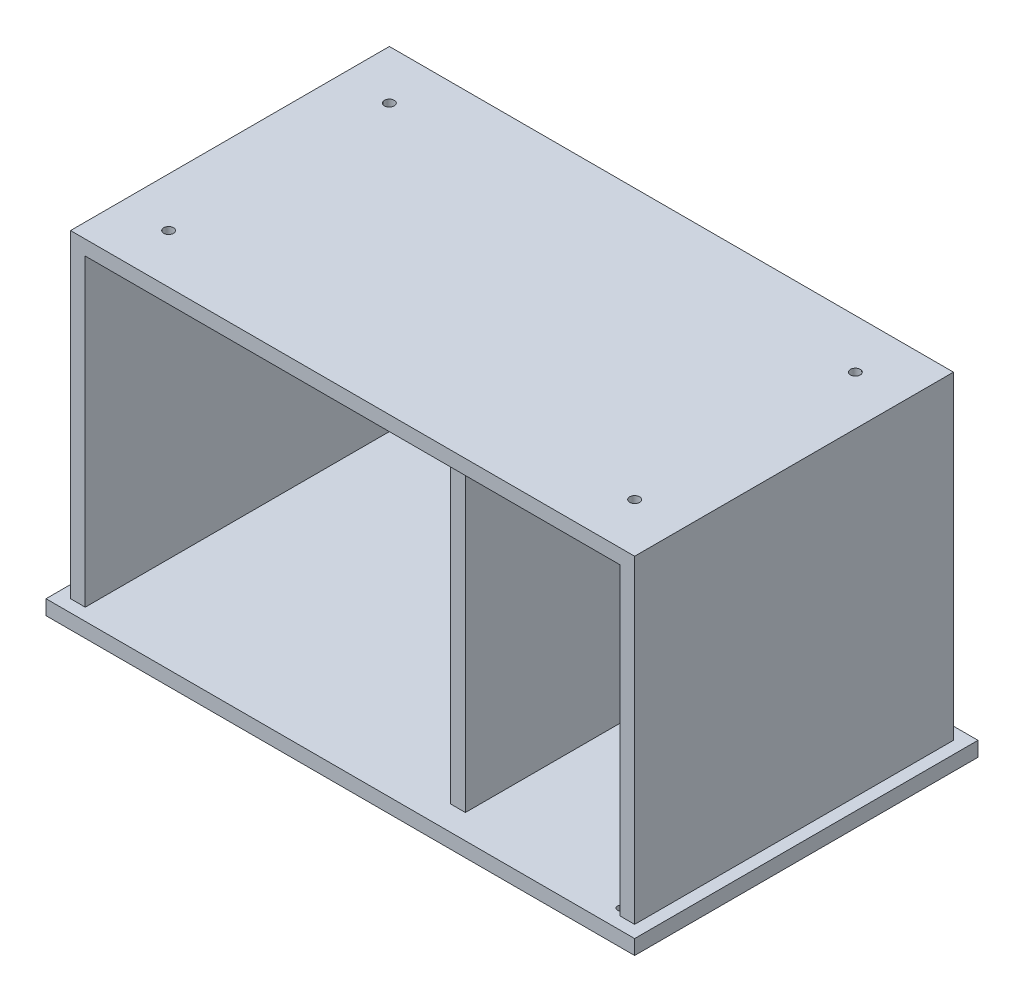
SolidWorks part; units mm, degrees
material "Oak"
ref_plane "Front Plane" through (0, 0, 0) normal (0, 0, 1) x (1, 0, 0)
ref_plane "Top Plane" through (0, 0, 0) normal (0, 1, 0) x (1, 0, 0)
ref_plane "Right Plane" through (0, 0, 0) normal (1, 0, 0) x (0, 0, -1)
sketch "Sketch1" plane through (0, 0, 0) normal (0, 1, 0) x (1, 0, 0)
  line L0 (0, 0) -> (609.6, 0)
  line L1 (609.6, 0) -> (609.6, 355.6)
  line L2 (609.6, 355.6) -> (0, 355.6)
  line L3 (0, 355.6) -> (0, 0)
  dimension "D1" = 609.6
  dimension "D2" = 355.6
extrude "Boss-Extrude1" add sketch "Sketch1" along normal blind 15.24
ref_plane "Plane1" through (0, 0, 0) normal (0, -1, 0) x (-1, 0, 0)
sketch "Sketch2" plane through (0, 0, 0) normal (0, -1, 0) x (-1, 0, 0)
  line L0 (-609.6, 0) -> (-609.6, 355.6) construction
  line L3 (-609.6, 355.6) -> (0, 355.6) construction
  line L4 (-304.8, 355.6) -> (-304.8, 0) construction
  line L6 (0, 0) -> (-609.6, 0) construction
  circle A0 centre (-558.8, 50.8) radius 15.24
  circle A1 centre (-558.8, 304.8) radius 15.24
  circle A2 centre (-50.8, 50.8) radius 15.24
  circle A3 centre (-50.8, 304.8) radius 15.24
  dimension "D1" = 254
  dimension "D4" = 30.48
  dimension "D5" = 30.48
  dimension "D6" = 508
  dimension "D2" = 50.8
  dimension "D3" = 50.8
extrude "Cut-Extrude1" cut sketch "Sketch2" against normal blind 3.81
ref_plane "Plane2" through (0, 15.24, 0) normal (0, 1, 0) x (1, 0, 0)
ref_plane "Plane3" through (0, 15.24, 0) normal (0, 1, 0) x (1, 0, 0)
sketch "Sketch3" plane through (0, 15.24, 0) normal (0, 1, 0) x (1, 0, 0)
  line L1 (609.6, 355.6) -> (0, 355.6) construction
  line L4 (609.6, 0) -> (609.6, 355.6) construction
  line L6 (12.7, 342.9) -> (596.9, 342.9)
  line L7 (12.7, 342.9) -> (12.7, 12.7)
  line L8 (12.7, 12.7) -> (596.9, 12.7)
  line L9 (596.9, 342.9) -> (596.9, 12.7)
  line L10 (12.7, 342.9) -> (596.9, 12.7) construction
  line L11 (12.7, 12.7) -> (596.9, 342.9) construction
  point P6 (304.8, 177.8)
  point P11 (304.8, 177.8)
  dimension "D1" = 584.2
  dimension "13" = 330.2
  dimension "D3" = 12.7
  dimension "D4" = 12.7
  dimension "D5" = 304.8
extrude "Boss-Extrude2" add sketch "Sketch3" along normal blind 330.2
ref_plane "Plane4" through (0, 0, -12.7) normal (0, 0, 1) x (1, 0, 0)
sketch "Sketch4" plane through (0, 0, -12.7) normal (0, 0, 1) x (1, 0, 0)
  line L1 (12.7, 345.44) -> (596.9, 345.44) construction
  line L2 (581.66, 15.24) -> (408.94, 15.24)
  line L3 (408.94, 330.2) -> (581.66, 330.2)
  line L4 (0, 15.24) -> (609.6, 15.24) construction
  line L5 (581.66, 15.24) -> (581.66, 330.2)
  line L11 (408.94, 15.24) -> (408.94, 330.2)
  line L12 (596.9, 345.44) -> (596.9, 15.24) construction
  line L13 (12.7, 345.44) -> (12.7, 15.24) construction
  line L14 (12.7, 15.24) -> (596.9, 15.24) construction
  line L18 (393.7, 330.2) -> (393.7, 15.24)
  line L21 (27.94, 330.2) -> (393.7, 330.2)
  line L22 (27.94, 330.2) -> (27.94, 15.24)
  line L23 (27.94, 15.24) -> (393.7, 15.24)
  dimension "D1" = 15.24
  dimension "D2" = 15.24
  dimension "D3" = 15.24
  dimension "D4" = 15.24
  dimension "D5" = 15.24
  dimension "D6" = 314.96
  dimension "D7" = 365.76
  dimension "D8" = 172.72
extrude "Cut-Extrude2" cut sketch "Sketch4" against normal blind 330.2
ref_plane "Plane5" through (0, 0, -12.7) normal (0, 0, 1) x (1, 0, 0)
sketch "Sketch6" plane through (0, 0, -12.7) normal (0, 0, 1) x (1, 0, 0)
  line L0 (393.7, 330.2) -> (408.94, 330.2)
  line L1 (408.94, 330.2) -> (408.94, 15.24)
  line L2 (408.94, 15.24) -> (393.7, 15.24)
  line L3 (393.7, 15.24) -> (393.7, 330.2)
extrude "Cut-Extrude4" cut sketch "Sketch6" against normal blind 12.7
sketch "Sketch7" plane through (0, 0, -12.7) normal (0, 0, 1) x (1, 0, 0)
  line L1 (12.7, 345.44) -> (596.9, 345.44)
  line L2 (12.7, 345.44) -> (12.7, 15.24)
  line L3 (12.7, 15.24) -> (596.9, 15.24)
  line L4 (596.9, 345.44) -> (596.9, 15.24)
ref_plane "Plane6" through (0, 0, -342.9) normal (0, 0, -1) x (-1, 0, 0)
sketch "Sketch8" plane through (0, 0, -342.9) normal (0, 0, -1) x (-1, 0, 0)
  line L1 (-12.7, 15.24) -> (-596.9, 15.24)
  line L2 (-12.7, 15.24) -> (-12.7, 345.44)
  line L3 (-12.7, 345.44) -> (-596.9, 345.44)
  line L4 (-596.9, 15.24) -> (-596.9, 345.44)
extrude "Boss-Extrude4" add sketch "Sketch8" against normal blind 12.7
ref_plane "Plane9" through (0, 15.24, 0) normal (0, 1, 0) x (1, 0, 0)
sketch "Sketch11" plane through (0, 15.24, 0) normal (0, 1, 0) x (1, 0, 0)
  line L0 (12.7, 12.7) -> (596.9, 12.7) construction
  line L2 (581.66, 330.2) -> (581.66, 12.7) construction
  circle A0 centre (575.31, 20.32) radius 3.81
  dimension "D1" = 7.62
  dimension "D2" = 7.62
  dimension "D3" = 6.35
extrude "Cut-Extrude5" cut sketch "Sketch11" against normal blind 5.08
ref_plane "Plane10" through (0, 330.2, 0) normal (0, -1, 0) x (-1, 0, 0)
sketch "Sketch12" plane through (0, 330.2, 0) normal (0, -1, 0) x (-1, 0, 0)
  line L0 (-581.66, 12.7) -> (-27.94, 12.7) construction
  line L2 (-581.66, 330.2) -> (-581.66, 12.7) construction
  circle A0 centre (-575.31, 20.32) radius 3.81
  dimension "D1" = 7.62
  dimension "D2" = 7.62
  dimension "D3" = 6.35
extrude "Cut-Extrude6" cut sketch "Sketch12" against normal blind 5.08
ref_plane "Plane11" through (0, 345.44, 0) normal (0, 1, 0) x (-1, 0, 0)
sketch "Sketch13" plane through (0, 345.44, 0) normal (0, 1, 0) x (-1, 0, 0)
  line L0 (-12.7, -12.7) -> (-596.9, -12.7) construction
  line L4 (-596.9, -12.7) -> (-596.9, -342.9) construction
  line L7 (-12.7, -342.9) -> (-12.7, -12.7) construction
  line L8 (-181.61, -342.9) -> (181.61, -342.9) construction
  circle A0 centre (-546.1, -63.5) radius 5.08
  circle A1 centre (-63.5, -63.5) radius 5.08
  circle A2 centre (-63.5, -292.1) radius 5.08
  circle A3 centre (-546.1, -292.1) radius 5.08
  dimension "D1" = 10.16
  dimension "D5" = 10.16
  dimension "D8" = 10.16
  dimension "D11" = 10.16
  dimension "D2" = 50.8
  dimension "D3" = 50.8
  dimension "D4" = 482.6
  dimension "D6" = 50.8
  dimension "D7" = 228.6
  dimension "D9" = 50.8
  dimension "D10" = 482.6
  dimension "D12" = 50.8
extrude "Cut-Extrude7" cut sketch "Sketch13" against normal blind 12.7
